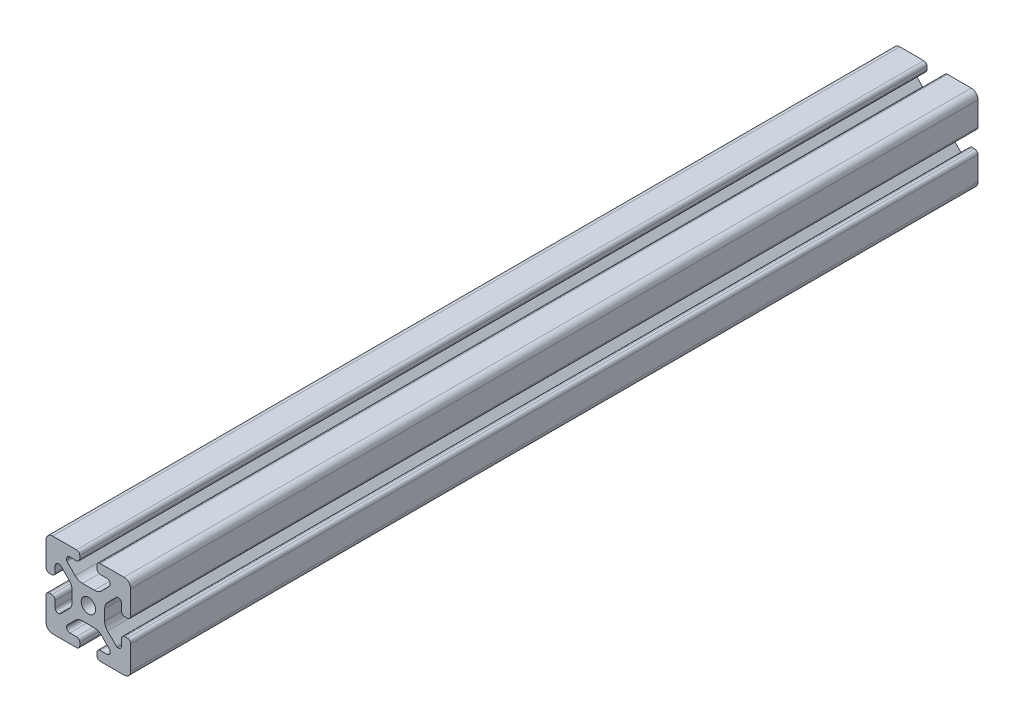
SolidWorks part; units mm, degrees
material "6105-T5 Aluminum"
ref_plane "Front Plane" through (0, 0, 0) normal (0, 0, 1) x (1, 0, 0)
ref_plane "Top Plane" through (0, 0, 0) normal (0, 1, 0) x (1, 0, 0)
ref_plane "Right Plane" through (0, 0, 0) normal (1, 0, 0) x (0, 0, -1)
sketch "Sketch1" plane through (0, 0, 0) normal (0, 0, 1) x (1, 0, 0)
  line L0 (0, 19.7407) -> (0, -19.7407) construction
  line L1 (19.0335, 0) -> (-20.7246, 0) construction
  line L2 (-8.715, -15.5246) -> (-5.63, -15.5246)
  line L3 (-10.285, -13.9546) -> (-10.285, -13.4925)
  line L4 (-6.2171, -9.1098) -> (-10.0624, -12.9551)
  line L5 (2.7773, -7.685) -> (-2.7773, -7.685)
  line L6 (10.0624, -12.9551) -> (6.2171, -9.1098)
  line L7 (10.285, -13.9546) -> (10.285, -13.4925)
  line L8 (5.63, -15.5246) -> (8.715, -15.5246)
  line L9 (4.06, -18.43) -> (4.06, -17.0946)
  line L10 (-4.06, -18.43) -> (-4.06, -17.0946)
  line L11 (15.68, -8.7154) -> (15.68, -5.63)
  line L12 (-14.11, -10.2854) -> (-13.8169, -10.2854)
  line L13 (20, -16.83) -> (20, -5.63)
  line L14 (20, 5.63) -> (20, 13.0011)
  line L15 (-16.83, 20) -> (-5.63, 20)
  line L16 (5.63, 20) -> (12.9796, 20)
  line L18 (-8.715, 15.5246) -> (-5.63, 15.5246)
  line L19 (-20, -17.0184) -> (-20, -5.7579)
  line L20 (-20, 5.573) -> (-20, 13.0045)
  line L21 (-15.68, -8.7154) -> (-15.68, -5.7579)
  line L23 (-16.6746, -20) -> (-5.63, -20)
  line L24 (5.63, -20) -> (13, -20)
  line L53 (14.11, -10.2854) -> (13.6201, -10.2854)
  line L54 (13.1637, -9.947) -> (9.0762, -5.8595)
  line L55 (7.685, -2.5008) -> (7.685, 2.5008)
  line L56 (9.0762, 5.8595) -> (13.2795, 10.0628)
  line L57 (13.8169, 10.2854) -> (14.11, 10.2854)
  line L58 (15.68, 8.7154) -> (15.68, 5.63)
  line L59 (17.25, 4.06) -> (18.43, 4.06)
  line L61 (20, 13.0011) -> (20, 16.83)
  line L62 (16.83, 20) -> (12.9796, 20)
  line L64 (4.06, 18.43) -> (4.06, 17.0946)
  line L65 (5.63, 15.5246) -> (8.715, 15.5246)
  line L66 (10.285, 13.9546) -> (10.285, 13.4925)
  line L67 (10.0624, 12.9551) -> (6.2171, 9.1098)
  line L68 (2.7773, 7.685) -> (-2.7773, 7.685)
  line L69 (-6.2171, 9.1098) -> (-10.0624, 12.9551)
  line L70 (-10.285, 13.4925) -> (-10.285, 13.9546)
  line L72 (-4.06, 17.0946) -> (-4.06, 18.43)
  line L75 (-20, 16.83) -> (-20, 13.0045)
  line L77 (-18.43, 4.003) -> (-17.25, 4.003)
  line L78 (-15.68, 5.573) -> (-15.68, 8.4757)
  line L79 (-14.0552, 10.0447) -> (-13.7199, 10.033)
  line L80 (-13.0405, 9.8238) -> (-9.0762, 5.8595)
  line L81 (-7.685, 2.5008) -> (-7.685, -2.5008)
  line L82 (-9.0762, -5.8595) -> (-13.2795, -10.0628)
  line L85 (-17.25, -4.1204) -> (-18.43, -4.1204)
  line L100 (13, -20) -> (16.83, -20)
  line L103 (18.43, -4.06) -> (17.25, -4.06)
  arc A0 (-5.63, -15.5246) -> (-4.06, -17.0946) centre (-5.63, -17.0946) cw
  arc A1 (-8.715, -15.5246) -> (-10.285, -13.9546) centre (-8.715, -13.9546) cw
  arc A2 (-10.285, -13.4925) -> (-10.0624, -12.9551) centre (-9.525, -13.4925) cw
  arc A3 (-6.2171, -9.1098) -> (-2.7773, -7.685) centre (-2.7773, -12.5496) cw
  arc A4 (2.7773, -7.685) -> (6.2171, -9.1098) centre (2.7773, -12.5496) cw
  arc A5 (10.0624, -12.9551) -> (10.285, -13.4925) centre (9.525, -13.4925) cw
  arc A6 (10.285, -13.9546) -> (8.715, -15.5246) centre (8.715, -13.9546) cw
  arc A7 (4.06, -17.0946) -> (5.63, -15.5246) centre (5.63, -17.0946) cw
  arc A8 (5.63, -20) -> (4.06, -18.43) centre (5.63, -18.43) cw
  arc A9 (-4.06, -18.43) -> (-5.63, -20) centre (-5.63, -18.43) cw
  circle A45 centre (0, 0) radius 3.4
  arc A46 (17.25, -4.06) -> (15.68, -5.63) centre (17.25, -5.63) ccw
  arc A47 (14.11, -10.2854) -> (15.68, -8.7154) centre (14.11, -8.7154) ccw
  arc A48 (13.1637, -9.947) -> (13.6201, -10.2854) centre (13.8117, -9.55) ccw
  arc A49 (7.685, -2.5008) -> (9.0762, -5.8595) centre (12.435, -2.5008) ccw
  arc A50 (9.0762, 5.8595) -> (7.685, 2.5008) centre (12.435, 2.5008) ccw
  arc A51 (13.8169, 10.2854) -> (13.2795, 10.0628) centre (13.8169, 9.5254) ccw
  arc A52 (15.68, 8.7154) -> (14.11, 10.2854) centre (14.11, 8.7154) ccw
  arc A53 (15.68, 5.63) -> (17.25, 4.06) centre (17.25, 5.63) ccw
  arc A54 (18.43, 4.06) -> (20, 5.63) centre (18.43, 5.63) ccw
  arc A55 (20, 16.83) -> (16.83, 20) centre (16.83, 16.83) ccw
  arc A56 (5.63, 20) -> (4.06, 18.43) centre (5.63, 18.43) ccw
  arc A57 (4.06, 17.0946) -> (5.63, 15.5246) centre (5.63, 17.0946) ccw
  arc A58 (10.285, 13.9546) -> (8.715, 15.5246) centre (8.715, 13.9546) ccw
  arc A59 (10.0624, 12.9551) -> (10.285, 13.4925) centre (9.525, 13.4925) ccw
  arc A60 (2.7773, 7.685) -> (6.2171, 9.1098) centre (2.7773, 12.5496) ccw
  arc A61 (-6.2171, 9.1098) -> (-2.7773, 7.685) centre (-2.7773, 12.5496) ccw
  arc A62 (-10.285, 13.4925) -> (-10.0624, 12.9551) centre (-9.525, 13.4925) ccw
  arc A63 (-8.715, 15.5246) -> (-10.285, 13.9546) centre (-8.715, 13.9546) ccw
  arc A64 (-5.63, 15.5246) -> (-4.06, 17.0946) centre (-5.63, 17.0946) ccw
  arc A65 (-4.06, 18.43) -> (-5.63, 20) centre (-5.63, 18.43) ccw
  arc A66 (-16.83, 20) -> (-20, 16.83) centre (-16.83, 16.83) ccw
  arc A67 (-20, 5.573) -> (-18.43, 4.003) centre (-18.43, 5.573) ccw
  arc A68 (-17.25, 4.003) -> (-15.68, 5.573) centre (-17.25, 5.573) ccw
  arc A69 (-14.0552, 10.0447) -> (-15.68, 8.4757) centre (-14.11, 8.4757) ccw
  arc A70 (-13.0405, 9.8238) -> (-13.7199, 10.033) centre (-13.5779, 9.2864) ccw
  arc A71 (-7.685, 2.5008) -> (-9.0762, 5.8595) centre (-12.435, 2.5008) ccw
  arc A72 (-9.0762, -5.8595) -> (-7.685, -2.5008) centre (-12.435, -2.5008) ccw
  arc A73 (-13.8169, -10.2854) -> (-13.2795, -10.0628) centre (-13.8169, -9.5254) ccw
  arc A74 (-15.68, -8.7154) -> (-14.11, -10.2854) centre (-14.11, -8.7154) ccw
  arc A75 (-15.68, -5.7579) -> (-17.25, -4.1204) centre (-17.2485, -5.6904) ccw
  arc A76 (-18.43, -4.1204) -> (-20, -5.7579) centre (-18.4315, -5.6904) ccw
  arc A77 (-20, -17.0184) -> (-16.6746, -20) centre (-16.8354, -16.8341) ccw
  arc A88 (16.83, -20) -> (20, -16.83) centre (16.83, -16.83) ccw
  arc A89 (20, -5.63) -> (18.43, -4.06) centre (18.43, -5.63) ccw
  dimension "D2" = 6.8
  dimension "D7" = 20.57
  dimension "D1" = 40
  dimension "D3" = 4.32
  dimension "D4" = 15.37
  dimension "D5" = 20
  dimension "D6" = 4.32
  dimension "D9" = 15.37
extrude "Extrude1" add sketch "Sketch1" against normal blind 400
